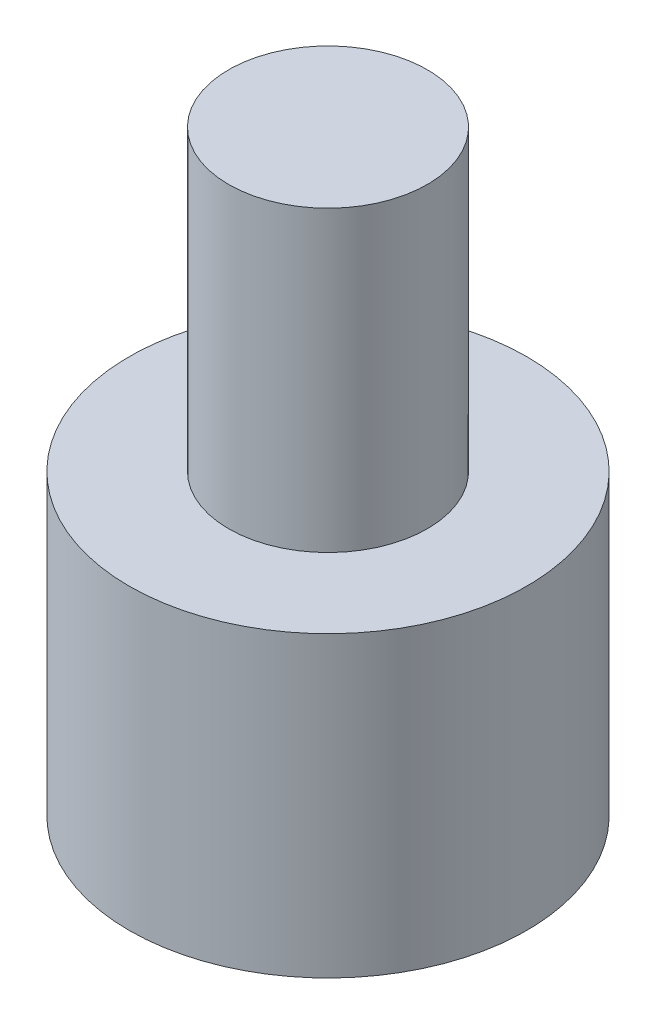
SolidWorks part; units mm, degrees
ref_plane "Front Plane" through (0, 0, 0) normal (0, 0, 1) x (1, 0, 0)
ref_plane "Top Plane" through (0, 0, 0) normal (0, 1, 0) x (1, 0, 0)
ref_plane "Right Plane" through (0, 0, 0) normal (1, 0, 0) x (0, 0, -1)
sketch "Sketch1" plane through (0, 0, 0) normal (0, 1, 0) x (1, 0, 0)
  circle A0 centre (0, 0) radius 20
  dimension "D1" = 40
extrude "Boss-Extrude3" add sketch "Sketch1" along normal blind 30
sketch "Sketch3" plane through (0, 30, 0) normal (0, 1, 0) x (1, 0, 0)
  circle A0 centre (0, 0) radius 10
  dimension "D1" = 20
extrude "Boss-Extrude4" add sketch "Sketch3" along normal blind 30
